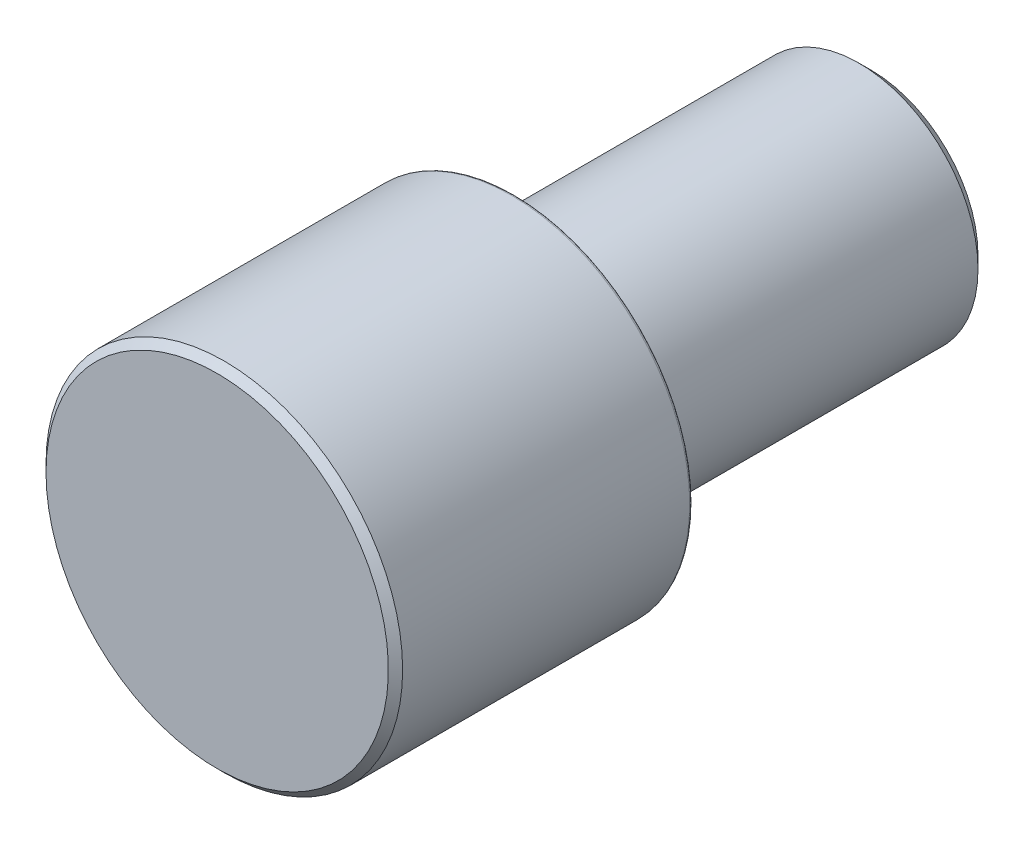
SolidWorks part; units mm, degrees
ref_plane "Front" through (0, 0, 0) normal (0, 0, 1) x (1, 0, 0)
ref_plane "Top" through (0, 0, 0) normal (0, 1, 0) x (1, 0, 0)
ref_plane "Right" through (0, 0, 0) normal (1, 0, 0) x (0, 0, -1)
sketch "Sketch0" plane through (0, 0, 0) normal (1, 0, 0) x (0, 0, -1)
  line L0 (-5, 0) -> (0, 0)
  line L1 (0, 0) -> (6, 0)
  line L2 (-12.7, 0) -> (49987.3, 0) construction
  line L3 (6, 0) -> (6, 2)
  line L4 (-5, 0) -> (-5, 3)
  line L5 (6, -2) -> (6, 2)
  line L6 (0, 0) -> (0, 3)
  point P10 (6, 0)
  point P13 (0, 3)
  dimension "Stud Length" = 6
  dimension "Stud Dia" = 4
  dimension "Dia" = 6
  dimension "Length" = 5
sketch "Sketch1" plane through (0, 0, 0) normal (1, 0, 0) x (0, 0, -1)
  line L0 (6, 0) -> (6, 2) construction
  line L1 (-5, 0) -> (-5, 3)
  line L2 (-5, 3) -> (-0.05, 3)
  line L3 (0, 2.95) -> (0, 2.1936)
  line L4 (0, 1.85) -> (0.3, 1.85)
  line L5 (0.3, 1.85) -> (0.3, 2)
  line L6 (0.3, 2) -> (6, 2)
  line L7 (6, 2) -> (6, 0)
  line L8 (6, 0) -> (-5, 0)
  arc A0 (0, 1.85) -> (-0.0375, 2.1452) centre (0, 2) cw
  arc A1 (-0.0375, 2.1452) -> (0, 2.1936) centre (-0.05, 2.1936) ccw
  arc A2 (-0.05, 3) -> (0, 2.95) centre (-0.05, 2.95) cw
  point P22 (0, 2.15)
  dimension "D4" = 0.05
  dimension "D5" = 0.05
  dimension "D2" = 0.3
  dimension "D1" = 0.15
  dimension "D3" = 0.3
revolve "Revolve1" add sketch "Sketch1" angle 360 about L2
chamfer "Chamfer1" distance 0.12 angle 45 1 edges at (3, 0, 5)
chamfer "Chamfer2" distance 0.2 angle 45 1 edges at (2, 0, -6)
equation "\"D1@Sketch1\"=\"D2@Sketch1\"/2"
equation "\"D2@Sketch1\" = \"Dia@Sketch0\" * .05"
equation "\"D1@Chamfer1\"=\"Dia@Sketch0\" * .02"
equation "\"D1@Chamfer2\" = \"Stud Dia@Sketch0\" * .05"
equation "\"D3@Sketch1\"=\"D1@Sketch1\"*2"
